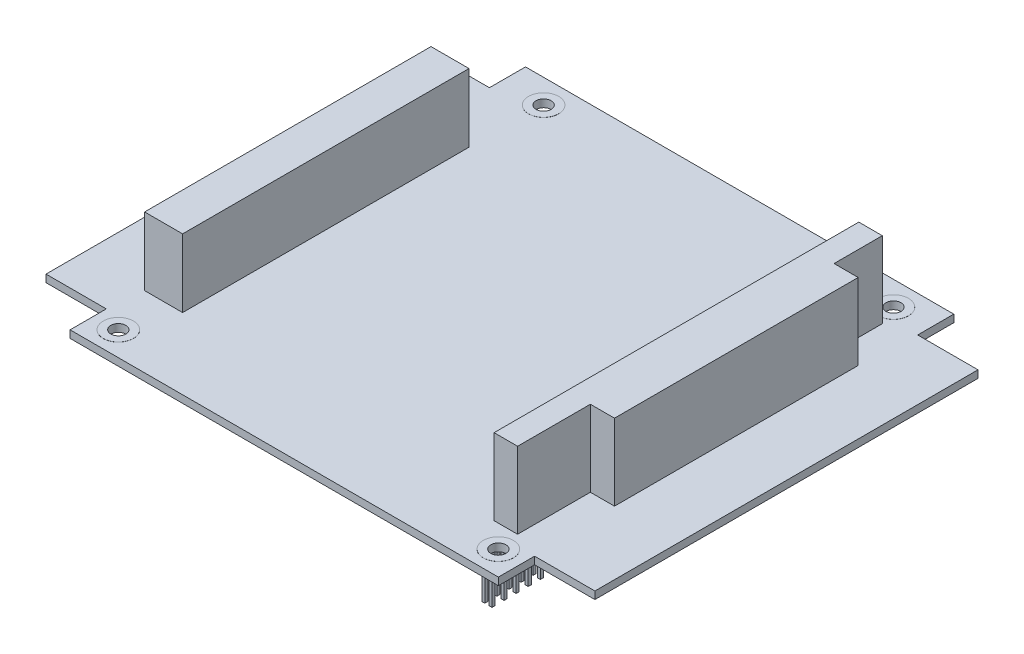
SolidWorks part; units mm, degrees
ref_plane "Plane1" through (0, 0, 0) normal (0, 0, 1) x (1, 0, 0)
ref_plane "Plane2" through (0, 0, 0) normal (0, 1, 0) x (1, 0, 0)
ref_plane "Plane3" through (0, 0, 0) normal (1, 0, 0) x (0, 0, -1)
sketch "Sketch1" plane through (0, 0, 0) normal (0, 1, 0) x (1, 0, 0)
  line L0 (-45.085, 47.945) -> (45.085, -47.945) construction
  line L1 (-45.085, 47.945) -> (45.085, 47.945)
  line L2 (-45.085, 47.945) -> (-45.085, 40.3434)
  line L3 (-45.085, -47.945) -> (45.085, -47.945)
  line L4 (45.085, 47.945) -> (45.085, 40.3434)
  line L5 (45.085, 40.3434) -> (57.785, 40.3434)
  line L6 (57.785, 40.3434) -> (57.785, -40.3181)
  line L7 (-57.785, 0.0126) -> (57.785, 0.0126) construction
  line L8 (0, 47.945) -> (0, -47.945) construction
  line L9 (45.085, -40.3181) -> (57.785, -40.3181)
  line L10 (-45.085, -40.3181) -> (-57.785, -40.3181)
  line L11 (-57.785, 40.3434) -> (-57.785, -40.3181)
  line L12 (-45.085, 40.3434) -> (-57.785, 40.3434)
  line L13 (45.085, -40.3181) -> (45.085, -47.945)
  line L14 (-45.085, -40.3181) -> (-45.085, -47.945)
  point P14 (57.785, 0.0126)
  point P18 (-57.785, 0.0126)
  dimension "D1" = 95.89
  dimension "D2" = 90.17
  dimension "D3" = 12.7
extrude "Base-Extrude" add sketch "Sketch1" along normal blind 1.57
sketch "Sketch2" plane through (0, 1.57, 0) normal (0, 1, 0) x (-1, 0, 0)
  line L1 (45.085, 47.945) -> (-45.085, 47.945) construction
  line L2 (-45.085, 47.945) -> (-45.085, 40.3181) construction
  line L3 (45.085, 47.945) -> (-45.085, 47.945) construction
  line L4 (45.085, 40.3181) -> (45.085, 47.945) construction
  line L6 (45.085, -47.945) -> (45.085, -40.3434) construction
  circle A0 centre (36.195, -42.865) radius 1.59
  circle A1 centre (40.005, 42.865) radius 1.59
  circle A2 centre (-40.005, 42.865) radius 1.59
  circle A3 centre (-37.465, -42.865) radius 1.59
  dimension "D7" = 3.18
  dimension "D5" = 90.81
  dimension "D8" = 8.89
  dimension "D9" = 82.55
  dimension "D1" = 5.08
  dimension "D2" = 5.08
  dimension "D3" = 5.08
  dimension "D4" = 5.08
  dimension "D6" = 90.81
extrude "Mounting Holes" cut sketch "Sketch2" against normal through all
sketch "Sketch3" plane through (0, 1.57, 0) normal (0, 1, 0) x (-1, 0, 0)
  circle A0 centre (36.195, -42.865) radius 3.175
  circle A1 centre (-37.465, -42.865) radius 3.175
  circle A2 centre (-40.005, 42.865) radius 3.175
  circle A3 centre (40.005, 42.865) radius 3.175
  circle A4 centre (40.005, 42.865) radius 1.59 construction
  circle A5 centre (36.195, -42.865) radius 1.59 construction
  circle A6 centre (-37.465, -42.865) radius 1.59 construction
  circle A7 centre (-40.005, 42.865) radius 1.59 construction
  circle A8 centre (40.005, 42.865) radius 1.59
  circle A9 centre (-40.005, 42.865) radius 1.59
  circle A10 centre (-37.465, -42.865) radius 1.59
  circle A11 centre (36.195, -42.865) radius 1.59
  dimension "D1" = 6.35
extrude "Top Pads" add sketch "Sketch3" along normal blind 0.02
sketch "Sketch4" plane through (0, 0, 0) normal (0, -1, 0) x (1, 0, 0)
  circle A8 centre (-36.195, -42.865) radius 1.59 construction
  circle A9 centre (-36.195, -42.865) radius 3.175 construction
  circle A10 centre (37.465, -42.865) radius 1.59 construction
  circle A11 centre (37.465, -42.865) radius 3.175 construction
  circle A12 centre (40.005, 42.865) radius 1.59 construction
  circle A13 centre (40.005, 42.865) radius 3.175 construction
  circle A14 centre (-40.005, 42.865) radius 1.59 construction
  circle A15 centre (-40.005, 42.865) radius 3.175 construction
  circle A16 centre (-36.195, -42.865) radius 1.59
  circle A17 centre (-36.195, -42.865) radius 3.175
  circle A18 centre (37.465, -42.865) radius 1.59
  circle A19 centre (37.465, -42.865) radius 3.175
  circle A20 centre (40.005, 42.865) radius 1.59
  circle A21 centre (40.005, 42.865) radius 3.175
  circle A22 centre (-40.005, 42.865) radius 1.59
  circle A23 centre (-40.005, 42.865) radius 3.175
extrude "Bott Pads" add sketch "Sketch4" along normal blind 0.02
sketch "Sketch5" plane through (0, 1.57, 0) normal (0, 1, 0) x (-1, 0, 0)
  line L0 (-39.305, 22.795) -> (-39.305, 38.115)
  line L1 (-34.355, -38.675) -> (-39.305, -38.675)
  line L2 (-34.355, -38.675) -> (-34.355, 38.115)
  line L3 (-34.355, 38.115) -> (-39.305, 38.115)
  line L4 (-39.305, -38.675) -> (-39.305, -28.515)
  line L5 (-39.305, -28.515) -> (-44.385, -28.515)
  line L6 (45.085, 47.945) -> (-45.085, 47.945) construction
  line L7 (-39.305, 22.795) -> (-44.385, 22.795)
  line L8 (-44.385, -28.515) -> (-44.385, 22.795)
  line L9 (-57.785, 40.3181) -> (-57.785, -40.3434) construction
  dimension "D1" = 15.32
  dimension "D2" = 66.63
  dimension "D3" = 76.79
  dimension "D4" = 10.03
  dimension "D5" = 4.95
  dimension "D6" = 9.83
  dimension "D7" = 13.4
extrude "ISA Cnct" add sketch "Sketch5" along normal blind 16.05
sketch "Sketch6" plane through (0, 1.57, 0) normal (0, 1, 0) x (-1, 0, 0)
  line L0 (45.085, 47.945) -> (-45.085, 47.945) construction
  line L1 (44.385, -27.345) -> (36.385, -27.345)
  line L2 (44.385, -27.345) -> (44.385, 32.955)
  line L3 (44.385, 32.955) -> (36.385, 32.955)
  line L4 (36.385, -27.345) -> (36.385, 32.955)
  line L5 (-57.785, 40.3181) -> (-57.785, -40.3434) construction
  dimension "D1" = 14.99
  dimension "D2" = 102.17
  dimension "D3" = 8
  dimension "D4" = 60.3
extrude "PCI Cnct" add sketch "Sketch6" along normal blind 14.35
sketch "Sketch7" plane through (0, 0, 0) normal (0, -1, 0) x (1, 0, 0)
  line L0 (-44.385, 2.805) -> (-36.385, 2.805) construction
  line L1 (-46.035, 34.48) -> (-34.735, 34.48)
  line L2 (-46.035, 34.48) -> (-46.035, -28.87)
  line L3 (-46.035, -28.87) -> (-34.735, -28.87)
  line L4 (-34.735, 34.48) -> (-34.735, -28.87)
  line L5 (-44.64, 33.285) -> (-36.13, 33.285)
  line L6 (-44.64, 33.285) -> (-44.64, -27.675)
  line L7 (-44.64, -27.675) -> (-36.13, -27.675)
  line L8 (-36.13, 33.285) -> (-36.13, -27.675)
  line L9 (-44.385, -27.345) -> (-44.385, 32.955) construction
  line L10 (-36.385, -27.345) -> (-36.385, 32.955) construction
  line L11 (-40.385, 32.955) -> (-40.385, -27.345) construction
  line L12 (-44.385, 32.955) -> (-36.385, 32.955) construction
  line L13 (-44.385, -27.345) -> (-36.385, -27.345) construction
  point P8 (-40.385, 33.285)
  point P21 (-40.385, -27.675)
  point P22 (-44.64, 2.805)
  point P23 (-46.035, 2.805)
  point P24 (-40.385, 34.48)
  dimension "D1" = 63.35
  dimension "D2" = 11.3
  dimension "D3" = 8.51
  dimension "D4" = 60.96
extrude "PCI Cnct Shroud" add sketch "Sketch7" along normal blind 11.18
sketch "Sketch8" plane through (0, 0, 0) normal (0, -1, 0) x (1, 0, 0)
  line L1 (35.555, -36.835) -> (36.195, -36.835)
  line L2 (35.555, -36.835) -> (35.555, -37.475)
  line L3 (35.555, -37.475) -> (36.195, -37.475)
  line L4 (36.195, -36.835) -> (36.195, -37.475)
  line L5 (37.075, -36.835) -> (37.715, -36.835)
  line L6 (37.075, -36.835) -> (37.075, -37.475)
  line L7 (37.075, -37.475) -> (37.715, -37.475)
  line L8 (37.715, -36.835) -> (37.715, -37.475)
  line L9 (35.555, -37.155) -> (36.195, -37.155) construction
  line L10 (35.875, -36.835) -> (35.875, -37.475) construction
  line L11 (39.305, -38.675) -> (34.355, -38.675) construction
  line L12 (34.355, -38.675) -> (34.355, 38.115) construction
  line L13 (37.075, -37.155) -> (37.715, -37.155) construction
  line L14 (37.395, -36.835) -> (37.395, -37.475) construction
  point P12 (37.075, -37.155)
  dimension "D1" = 1.52
  dimension "D2" = 1.52
  dimension "D3" = 0.64
  dimension "D4" = 1.52
extrude "Bot ISA" add sketch "Sketch8" along normal blind 10.67
pattern_linear "LPattern1" count 32 spacing 2.54 along (0, 0, 1) of "Bot ISA"
sketch "Sketch9" plane through (0, 0, 0) normal (0, -1, 0) x (1, 0, 0)
  line L0 (37.715, -37.475) -> (37.715, -36.835) construction
  line L1 (40.005, -26.675) -> (40.645, -26.675)
  line L2 (40.005, -26.675) -> (40.005, -27.315)
  line L3 (40.005, -27.315) -> (40.645, -27.315)
  line L4 (40.645, -26.675) -> (40.645, -27.315)
  line L5 (42.545, -26.675) -> (43.185, -26.675)
  line L6 (42.545, -26.675) -> (42.545, -27.315)
  line L7 (42.545, -27.315) -> (43.185, -27.315)
  line L8 (43.185, -26.675) -> (43.185, -27.315)
  line L9 (44.385, -28.515) -> (39.305, -28.515) construction
  line L10 (42.545, -26.995) -> (43.185, -26.995) construction
  line L11 (40.005, -26.995) -> (40.645, -26.995) construction
  line L12 (40.325, -26.675) -> (40.325, -27.315) construction
  line L13 (42.865, -26.675) -> (42.865, -27.315) construction
  line L14 (44.385, 22.795) -> (44.385, -28.515) construction
  point P10 (42.865, -27.315)
  dimension "D1" = 1.52
  dimension "D2" = 2.54
  dimension "D3" = 1.52
extrude "Boss-Extrude7" add sketch "Sketch9" along normal up to surface (10.67 mm away)
pattern_linear "LPattern2" count 20 spacing 2.54 along (0, 0, 1) of "Boss-Extrude7"
sketch "Sketch10" plane through (0, 0, 0) normal (0, -1, 0) x (1, 0, 0)
  line L0 (-43.395, -25.925) -> (-43.395, -25.425) construction
  line L1 (-43.645, -25.925) -> (-43.145, -25.925)
  line L2 (-43.645, -25.925) -> (-43.645, -25.425)
  line L3 (-43.645, -25.425) -> (-43.145, -25.425)
  line L4 (-43.145, -25.925) -> (-43.145, -25.425)
  line L5 (-43.645, -25.675) -> (-43.145, -25.675) construction
  line L6 (-44.64, -27.675) -> (-36.13, -27.675) construction
  line L9 (-46.035, 34.48) -> (-46.035, -28.87) construction
  dimension "D1" = 2
  dimension "D2" = 2.64
  dimension "D3" = 0.5
extrude "PCI Base" add sketch "Sketch10" along normal blind 10.41
pattern_linear "LPattern3" count 30 spacing 2 along (0, 0, 1) of "PCI Base"
pattern_linear "LPattern4" count 4 spacing 2 along (1, 0, 0) of "LPattern3", "PCI Base"
